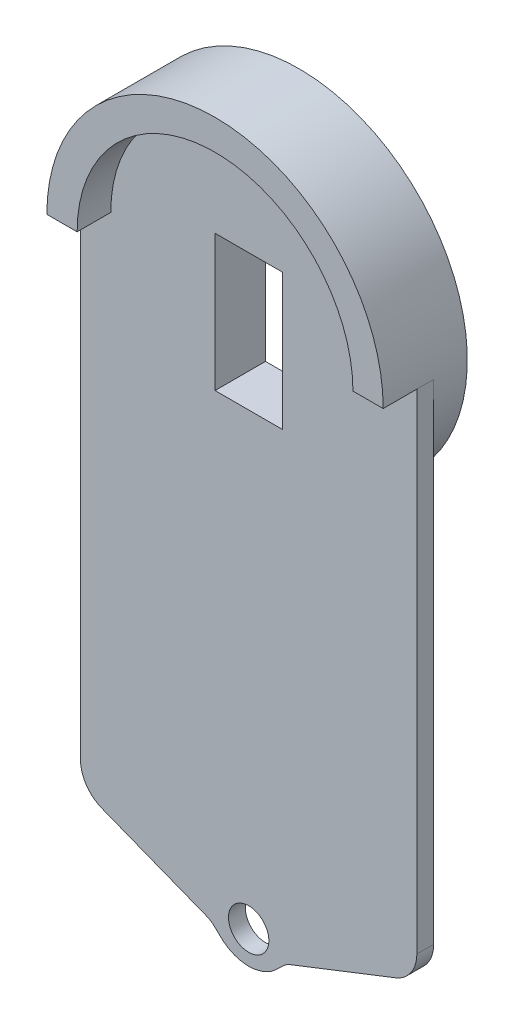
SolidWorks part; units mm, degrees
ref_plane "Alzado" through (0, 0, 0) normal (0, 0, 1) x (1, 0, 0)
ref_plane "Planta" through (0, 0, 0) normal (0, 1, 0) x (1, 0, 0)
ref_plane "Vista lateral" through (0, 0, 0) normal (1, 0, 0) x (0, 0, -1)
sketch "Croquis1" plane through (0, 0, 0) normal (0, 0, 1) x (1, 0, 0)
  line L12 (-50, 164) -> (-50, 11.7392)
  line L13 (13.7873, -2.4311) -> (20, 0)
  line L16 (-13.7873, -2.4311) -> (-20, 0)
  line L17 (-20, 0) -> (-50, 11.7392)
  line L18 (20, 0) -> (50, 11.7392)
  line L19 (50, 164) -> (50, 11.7392)
  circle A12 centre (0, 0) radius 6
  arc A15 (50, 164) -> (-50, 164) centre (0, 164) ccw
  arc A16 (-8.8548, -5.6773) -> (8.8548, -5.6773) centre (0, 2.4216) ccw
  spline S3 degree 3 poles (8.8548, -5.6773) (9.5176, -5.0903) (10.9007, -3.469) (12.7112, -2.8522) (13.7873, -2.4311) knots 0.517709 0.517709 0.517709 0.517709 0.741172 1 1 1 1
  spline S4 degree 3 poles (-8.8548, -5.6773) (-9.5176, -5.0903) (-10.9007, -3.469) (-12.7112, -2.8522) (-13.7873, -2.4311) knots 0.517709 0.517709 0.517709 0.517709 0.741172 1 1 1 1
  dimension "D1" = 12
  dimension "D6" = 100
  dimension "D3" = 20
  dimension "D4" = 164
extrude "Saliente-Extruir1" add sketch "Croquis1" along normal blind 5
fillet "Redondeo1" radius 10 1 edges at (50, 11.7392, 2.5)
fillet "Redondeo3" radius 10 1 edges at (-50, 11.7392, 2.5)
sketch "Croquis2" plane through (0, 0, 5) normal (0, 0, 1) x (1, 0, 0)
  circle A0 centre (0, 164) radius 50
  circle A1 centre (0, 164) radius 41
  dimension "D1" = 100
  dimension "D2" = 82
extrude "Saliente-Extruir3" add sketch "Croquis2" along normal blind 10
sketch "Croquis3" plane through (0, 0, 0) normal (0, 0, -1) x (-1, 0, 0)
  line L0 (-10, 174.1411) -> (10, 174.1411)
  line L1 (10, 174.1411) -> (10, 133.6411)
  line L2 (10, 133.6411) -> (-10, 133.6411)
  line L3 (-10, 133.6411) -> (-10, 174.1411)
extrude "Cortar-Extruir1" cut sketch "Croquis3" against normal blind 10
sketch "Croquis4" plane through (0, 0, 15) normal (0, 0, 1) x (1, 0, 0)
  line L0 (-41, 164) -> (-50, 164)
  line L1 (41, 164) -> (50, 164)
  arc A0 (-50, 164) -> (50, 164) centre (0, 164) ccw
  arc A1 (-41, 164) -> (41, 164) centre (0, 164) ccw
extrude "Cortar-Extruir2" cut sketch "Croquis4" against normal blind 10
sketch "Croquis5" plane through (0, 0, 0) normal (0, 0, -1) x (-1, 0, 0)
  line L0 (-10, 174.1411) -> (-8, 174.1411)
  line L1 (10, 174.1411) -> (10, 133.6411)
  line L2 (10, 133.6411) -> (-10, 133.6411)
  line L3 (-10, 133.6411) -> (-10, 174.1411)
  line L4 (8, 174.1411) -> (10, 174.1411)
  line L5 (-8, 194.1411) -> (8, 194.1411)
  line L6 (-8, 194.1411) -> (-8, 174.1411)
  line L7 (8, 194.1411) -> (8, 174.1411)
  circle A0 centre (0, 164) radius 50
  dimension "D1" = 16
extrude "Saliente-Extruir4" add sketch "Croquis5" along normal blind 10
